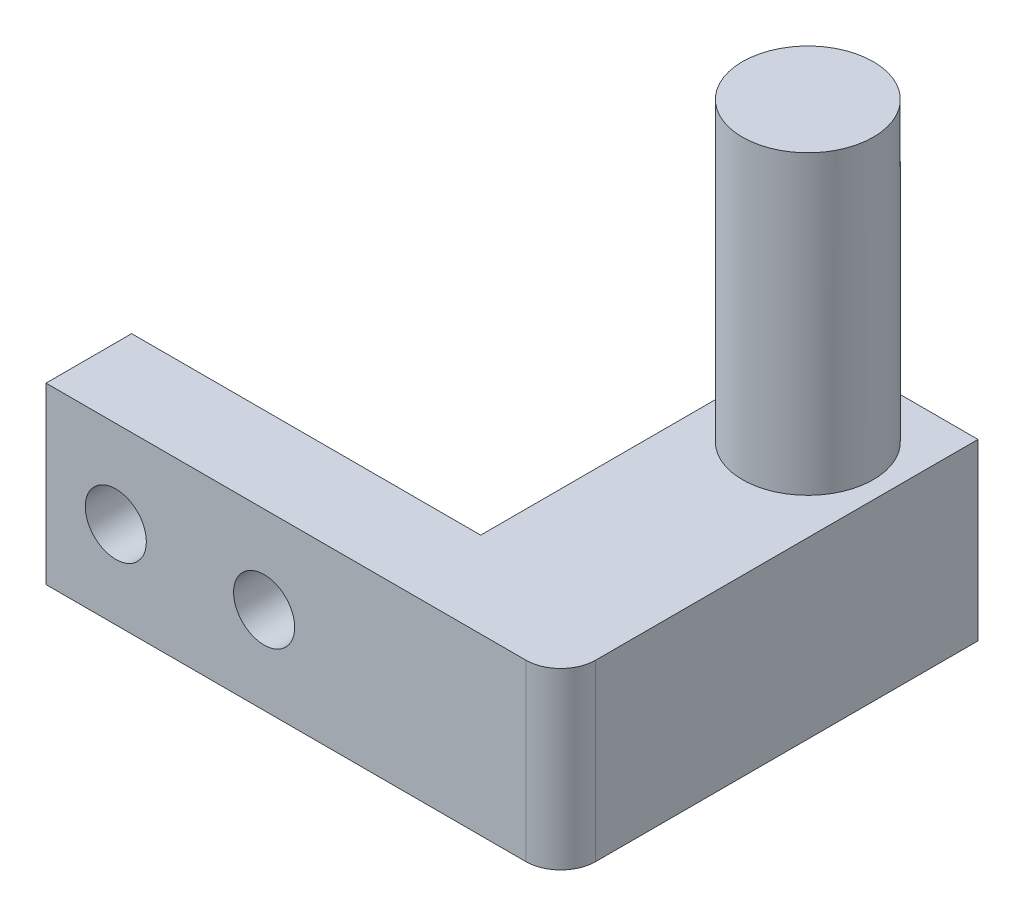
SolidWorks part; units mm, degrees
ref_plane "Front Plane" through (0, 0, 0) normal (0, 0, 1) x (1, 0, 0)
ref_plane "Top Plane" through (0, 0, 0) normal (0, 1, 0) x (1, 0, 0)
ref_plane "Right Plane" through (0, 0, 0) normal (1, 0, 0) x (0, 0, -1)
sketch "Sketch1" plane through (0, 0, 0) normal (0, 0, 1) x (1, 0, 0)
  line L1 (0, 0) -> (12.5, 0)
  line L2 (0, 0) -> (0, 10)
  line L3 (0, 10) -> (12.5, 10)
  line L4 (12.5, 0) -> (12.5, 10)
  dimension "D1" = 12.5
  dimension "D2" = 10
extrude "Boss-Extrude1" add sketch "Sketch1" along normal blind 10
sketch "Sketch2" plane through (0, 0, 0) normal (-1, 0, 0) x (0, 0, 1)
  line L0 (10, 0) -> (0, 0) construction
  line L1 (10, 0) -> (0, 0)
  line L2 (10, 0) -> (10, 10)
  line L3 (10, 10) -> (0, 10)
  line L4 (0, 0) -> (0, 10)
  line L5 (0, 10) -> (0, 0) construction
extrude "Boss-Extrude2" add sketch "Sketch2" along normal blind 5
sketch "Sketch3" plane through (0, 10, 0) normal (0, 1, 0) x (1, 0, 0)
  line L0 (12.5, -10) -> (12.5, 0) construction
  line L1 (12.5, 0) -> (-5, 0) construction
  circle A0 centre (3.75, -5) radius 3.75
  point P5 (12.5, -5)
  point P9 (3.75, 0)
  dimension "D1" = 7.5
extrude "Boss-Extrude3" add sketch "Sketch3" along normal blind 17
sketch "Sketch4" plane through (0, 10, 0) normal (0, 1, 0) x (1, 0, 0)
  line L0 (12.5, 0) -> (-5, 0) construction
  line L1 (12.5, 0) -> (8.5, 0)
  line L2 (12.5, 0) -> (12.5, -10)
  line L3 (12.5, -10) -> (8.5, -10)
  line L4 (8.5, 0) -> (8.5, -10)
  line L5 (12.5, -10) -> (-5, -10) construction
  line L6 (12.5, -10) -> (12.5, 0) construction
  line L7 (3.75, 0) -> (3.75, -3.716) construction
  line L8 (-5, -10) -> (-1, -10)
  line L9 (-5, 0) -> (-5, -10)
  line L10 (-5, 0) -> (-1, 0)
  line L11 (-1, 0) -> (-1, -10)
  dimension "D1" = 4
extrude "Cut-Extrude1" cut sketch "Sketch4" against normal through all
sketch "Sketch5" plane through (0, 0, 10) normal (0, 0, 1) x (1, 0, 0)
  line L0 (-1, 0) -> (8.5, 0) construction
  line L1 (8.5, 0) -> (-1, 0)
  line L2 (8.5, 0) -> (8.5, 10)
  line L3 (8.5, 10) -> (-1, 10)
  line L4 (-1, 0) -> (-1, 10)
  line L5 (-1, 0) -> (-1, 10) construction
  line L6 (8.5, 10) -> (-1, 10) construction
  line L7 (8.5, 0) -> (8.5, 10) construction
extrude "Boss-Extrude4" add sketch "Sketch5" along normal blind 12.5
sketch "Sketch6" plane through (8.5, 0, 0) normal (1, 0, 0) x (0, 0, -1)
  line L0 (0, 10) -> (-22.5, 10) construction
  line L1 (-22.5, 0) -> (-17.5, 0)
  line L2 (-22.5, 0) -> (-22.5, 10)
  line L3 (-22.5, 10) -> (-17.5, 10)
  line L4 (-17.5, 0) -> (-17.5, 10)
  line L5 (-22.5, 0) -> (-22.5, 10) construction
  line L6 (0, 0) -> (-22.5, 0) construction
  dimension "D1" = 5
extrude "Boss-Extrude5" add sketch "Sketch6" along normal blind 30
sketch "Sketch7" plane through (0, 0, 22.5) normal (0, 0, 1) x (1, 0, 0)
  line L0 (38.5, 10) -> (38.5, 0) construction
  circle A0 centre (22.5, 5) radius 1.75
  circle A1 centre (33.5, 5) radius 1.75
  point P6 (38.5, 5)
  dimension "D1" = 3.5
  dimension "D2" = 3.5
  dimension "D3" = 5
  dimension "D4" = 11
extrude "Cut-Extrude2" cut sketch "Sketch7" against normal through all
sketch "Sketch8" plane through (0, 10, 0) normal (0, 1, 0) x (1, 0, 0)
  line L0 (38.5, -22.5) -> (-1, -22.5) construction
  line L1 (38.5, -17.5) -> (8.5, -17.5)
  line L2 (38.5, -17.5) -> (38.5, -22.5)
  line L3 (38.5, -22.5) -> (8.5, -22.5)
  line L4 (8.5, -17.5) -> (8.5, -22.5)
  line L5 (8.5, 0) -> (8.5, -17.5) construction
extrude "Cut-Extrude4" cut sketch "Sketch8" against normal blind 10
sketch "Sketch10" plane through (0, 0, 22.5) normal (0, 0, 1) x (1, 0, 0)
  line L0 (8.5, 0) -> (8.5, 10) construction
  line L1 (8.5, 10) -> (-1, 10)
  line L2 (8.5, 10) -> (8.5, 0)
  line L3 (8.5, 0) -> (-1, 0)
  line L4 (-1, 10) -> (-1, 0)
  line L5 (-1, 0) -> (8.5, 0) construction
  line L6 (-1, 10) -> (-1, 0) construction
  line L7 (8.5, 10) -> (-1, 10) construction
extrude "Cut-Extrude6" cut sketch "Sketch10" against normal blind 3.49
sketch "Sketch11" plane through (0, 0, 19.01) normal (0, 0, 1) x (1, 0, 0)
  line L0 (8.5, 0) -> (8.5, 10) construction
  line L1 (8.5, 10) -> (-1, 10)
  line L2 (8.5, 10) -> (8.5, 0)
  line L3 (8.5, 0) -> (-1, 0)
  line L4 (-1, 10) -> (-1, 0)
  line L5 (-1, 10) -> (-1, 0) construction
  line L6 (8.5, 10) -> (-1, 10) construction
  line L7 (-1, 0) -> (8.5, 0) construction
extrude "Boss-Extrude6" add sketch "Sketch11" along normal blind 3.9
sketch "Sketch12" plane through (8.5, 0, 0) normal (1, 0, 0) x (0, 0, -1)
  line L0 (-22.91, 0) -> (-22.91, 10) construction
  line L1 (-22.91, 10) -> (-18.91, 10)
  line L2 (-22.91, 10) -> (-22.91, 0)
  line L3 (-22.91, 0) -> (-18.91, 0)
  line L4 (-18.91, 10) -> (-18.91, 0)
  line L5 (0, 10) -> (-22.91, 10) construction
  line L6 (0, 0) -> (-22.91, 0) construction
  dimension "D1" = 4
extrude "Boss-Extrude7" add sketch "Sketch12" along normal blind 20
sketch "Sketch13" plane through (0, 0, 0) normal (0, -1, 0) x (-1, 0, 0)
  line L0 (-28.5, -18.91) -> (-8.5, -18.91) construction
  line L1 (-8.5, -18.91) -> (-28.5, -18.91)
  line L2 (-8.5, -18.91) -> (-8.5, -19)
  line L3 (-8.5, -19) -> (-28.5, -19)
  line L4 (-28.5, -18.91) -> (-28.5, -19)
  line L5 (-28.5, -22.91) -> (-28.5, -18.91) construction
  line L6 (-8.5, 0) -> (-8.5, -18.91) construction
  dimension "D1" = 0.09
extrude "Cut-Extrude7" cut sketch "Sketch13" against normal through all
sketch "Sketch14" plane through (0, 0, 22.91) normal (0, 0, 1) x (1, 0, 0)
  line L0 (-1, 10) -> (-1, 0) construction
  line L1 (-1, 0) -> (28.5, 0) construction
  line L2 (28.5, 10) -> (28.5, 0) construction
  circle A0 centre (16, 5) radius 1.75
  circle A1 centre (24.5, 5) radius 1.75
  dimension "D1" = 3.5
  dimension "D4" = 3.5
  dimension "D2" = 17
  dimension "D3" = 5
  dimension "D5" = 4
extrude "Cut-Extrude8" cut sketch "Sketch14" against normal through all
sketch "Sketch15" plane through (0, 10, 0) normal (0, 1, 0) x (1, 0, 0)
  line L0 (28.5, -19) -> (28.5, -22.91) construction
  line L1 (28.5, -19) -> (8.5, -19)
  line L2 (28.5, -19) -> (28.5, -22.91)
  line L3 (28.5, -22.91) -> (8.5, -22.91)
  line L4 (8.5, -19) -> (8.5, -22.91)
  line L5 (28.5, -22.91) -> (-1, -22.91) construction
  line L6 (8.5, 0) -> (8.5, -19) construction
  line L7 (28.5, -19) -> (8.5, -19) construction
extrude "Cut-Extrude9" cut sketch "Sketch15" against normal through all
sketch "Sketch16" plane through (-1, 0, 0) normal (-1, 0, 0) x (0, 0, 1)
  line L0 (22.91, 0) -> (0, 0) construction
  line L1 (22.91, 0) -> (19, 0)
  line L2 (22.91, 0) -> (22.91, 10)
  line L3 (22.91, 10) -> (19, 10)
  line L4 (19, 0) -> (19, 10)
  line L5 (22.91, 10) -> (0, 10) construction
  line L6 (22.91, 10) -> (22.91, 0) construction
  dimension "D1" = 3.91
extrude "Boss-Extrude8" add sketch "Sketch16" along normal blind 20
sketch "Sketch17" plane through (0, 0, 22.91) normal (0, 0, 1) x (1, 0, 0)
  line L0 (8.5, 0) -> (8.5, 10) construction
  line L1 (-21, 0) -> (-21, 10) construction
  circle A0 centre (-17, 5) radius 1.75
  circle A1 centre (-8.5, 5) radius 1.75
  point P9 (-21, 5)
  dimension "D1" = 3.5
  dimension "D2" = 3.5
  dimension "D3" = 17
  dimension "D4" = 4
extrude "Cut-Extrude10" cut sketch "Sketch17" against normal blind 20
sketch "Sketch18" plane through (0, 0, 22.91) normal (0, 0, 1) x (1, 0, 0)
  line L0 (-21, 0) -> (-21, 10) construction
  line L1 (-21, 0) -> (8.5, 0)
  line L2 (-21, 0) -> (-21, 10)
  line L3 (-21, 10) -> (8.5, 10)
  line L4 (8.5, 0) -> (8.5, 10)
  line L5 (8.5, 10) -> (-21, 10) construction
  line L6 (8.5, 0) -> (8.5, 10) construction
  line L7 (-21, 0) -> (8.5, 0) construction
  circle A0 centre (-17, 5) radius 1.75
  circle A1 centre (-8.5, 5) radius 1.75
  circle A4 centre (-8.5, 5) radius 1.75 construction
  circle A5 centre (-17, 5) radius 1.75 construction
extrude "Boss-Extrude9" add sketch "Sketch18" along normal blind 1
fillet "Fillet1" radius 2 1 edges at (8.5, 5, 23.91)
